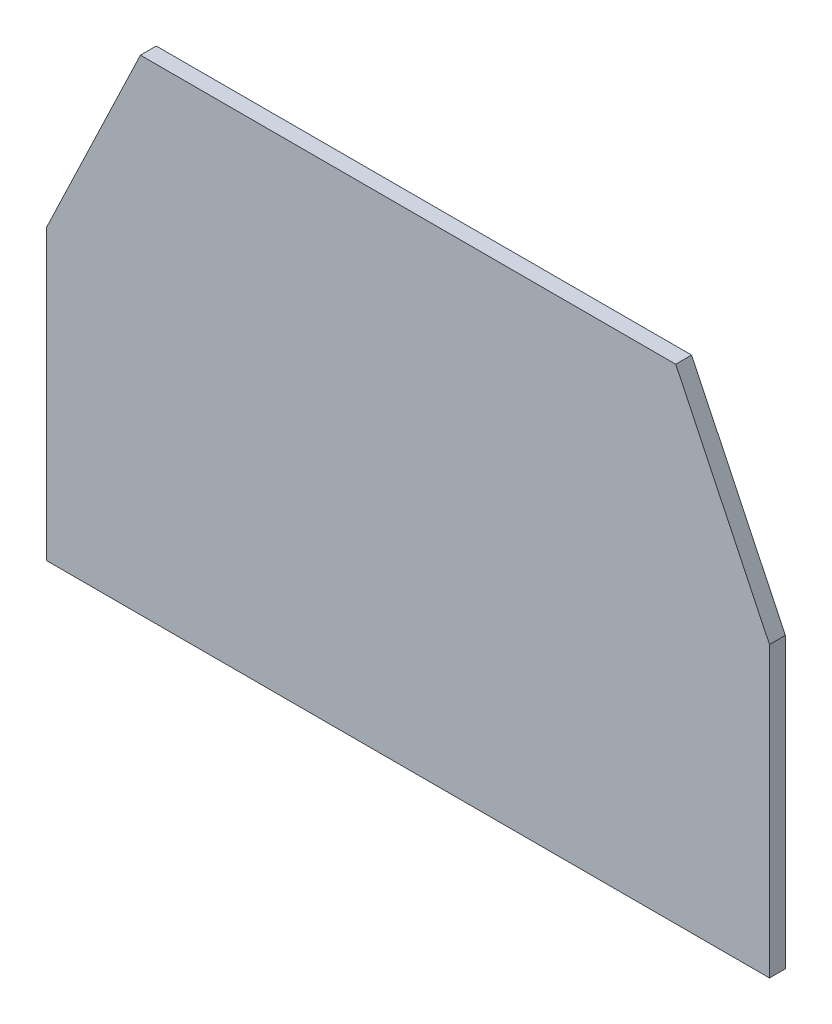
SolidWorks part; units mm, degrees
ref_plane "Ebene vorne" through (0, 0, 0) normal (0, 0, 1) x (1, 0, 0)
ref_plane "Ebene oben" through (0, 0, 0) normal (0, 1, 0) x (1, 0, 0)
ref_plane "Ebene rechts" through (0, 0, 0) normal (1, 0, 0) x (0, 0, -1)
sketch "Skizze1" plane through (0, 0, 0) normal (0, 0, 1) x (1, 0, 0)
  line L2 (341.8583, -194.3676) -> (-341.8583, -194.3676)
  line L11 (-341.8583, -194.3676) -> (-341.8583, 78.7946)
  line L14 (-341.8583, 78.7946) -> (-253.157, 264.0237)
  line L15 (253.157, 264.0237) -> (-253.157, 264.0237)
  line L32 (341.8583, 78.7946) -> (253.157, 264.0237)
  line L39 (341.8583, -194.3676) -> (341.8583, 78.7946)
extrude "Aufsatz-Linear austragen1" add sketch "Skizze1" along normal blind 15
